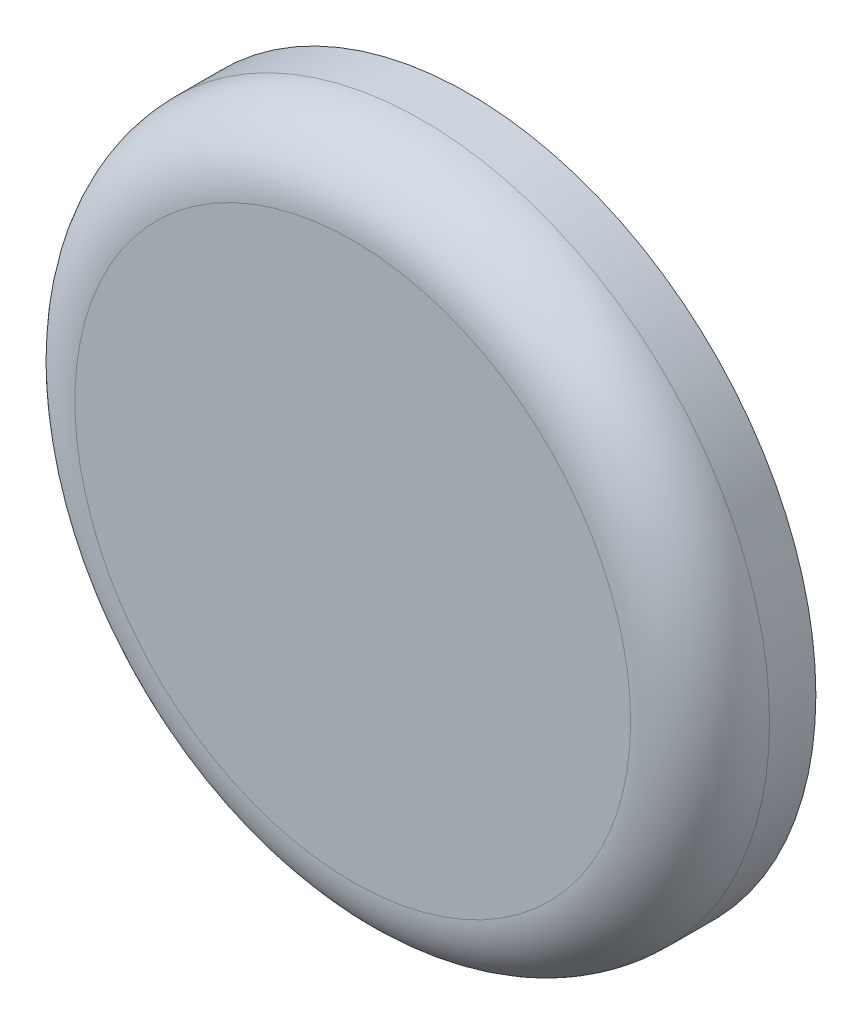
SolidWorks part; units mm, degrees
ref_plane "Front Plane" through (0, 0, 0) normal (0, 0, 1) x (1, 0, 0)
ref_plane "Top Plane" through (0, 0, 0) normal (0, 1, 0) x (1, 0, 0)
ref_plane "Right Plane" through (0, 0, 0) normal (1, 0, 0) x (0, 0, -1)
sketch "Sketch1" plane through (0, 0, 0) normal (0, 0, 1) x (1, 0, 0)
  circle A0 centre (0, 0) radius 15
  dimension "D1" = 30
extrude "Extrude1" add sketch "Sketch1" along normal blind 5
fillet "Fillet1" radius 3 1 edges at (15, 0, 5)
